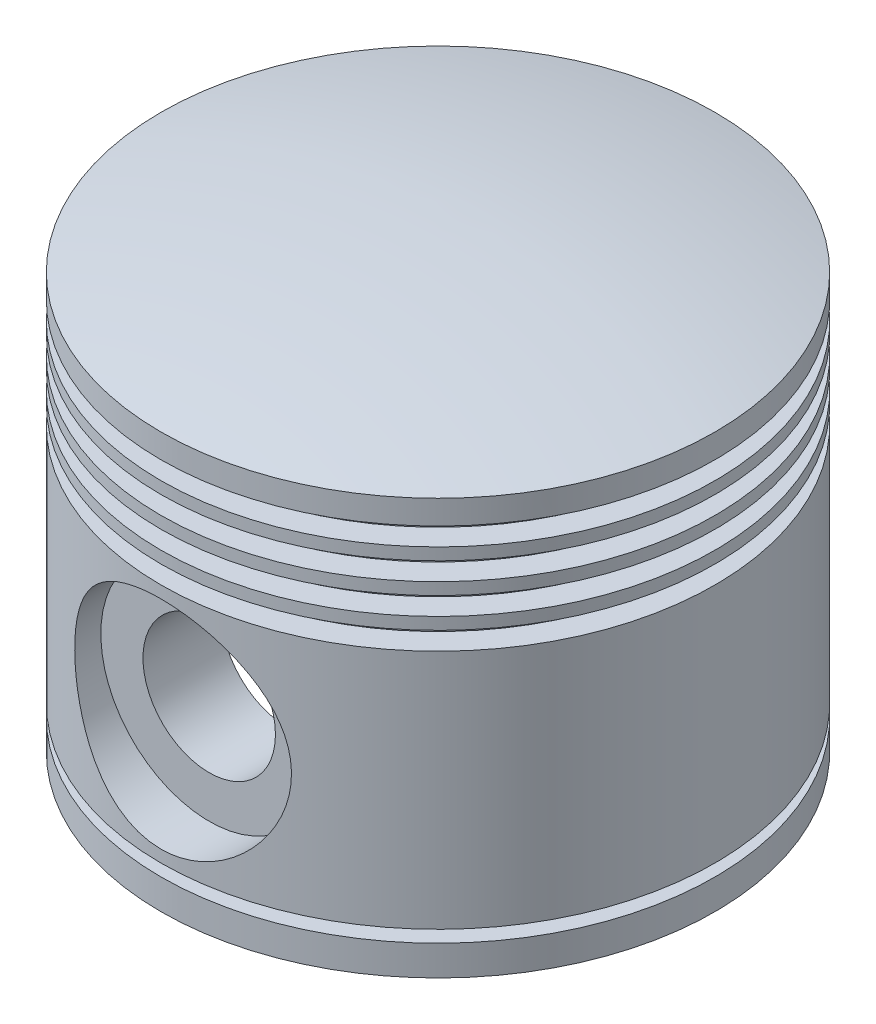
SolidWorks part; units mm, degrees
ref_plane "Front Plane" through (0, 0, 0) normal (0, 0, 1) x (1, 0, 0)
ref_plane "Top Plane" through (0, 0, 0) normal (0, 1, 0) x (1, 0, 0)
ref_plane "Right Plane" through (0, 0, 0) normal (1, 0, 0) x (0, 0, -1)
sketch "Sketch1" plane through (0, 0, 0) normal (0, 0, 1) x (1, 0, 0)
  line L0 (0, 165.4439) -> (0, -165.4439) construction
  line L1 (-46, 0) -> (46, 0) construction
  line L2 (-46, 0) -> (-46, 5)
  line L3 (-46, 5) -> (-42, 5)
  line L4 (-42, 5) -> (-42, 7)
  line L5 (-42, 7) -> (-46, 7)
  line L6 (-46, 7) -> (-46, 9)
  line L10 (-46, 45) -> (-46, 47)
  line L11 (-46, 47) -> (-42, 47)
  line L12 (-42, 47) -> (-42, 50)
  line L13 (-42, 50) -> (-46, 50)
  line L14 (-46, 50) -> (-46, 52)
  line L15 (-46, 52) -> (-42, 52)
  line L16 (-42, 52) -> (-42, 55)
  line L17 (-42, 55) -> (-46, 55)
  line L18 (-46, 55) -> (-46, 57)
  line L19 (-46, 57) -> (-42, 57)
  line L20 (-42, 57) -> (-42, 60)
  line L21 (-42, 60) -> (-46, 60)
  line L22 (-46, 60) -> (-46, 62)
  line L23 (-46, 62) -> (-42, 62)
  line L24 (-42, 62) -> (-42, 65)
  line L25 (-42, 65) -> (-46, 65)
  line L26 (-46, 65) -> (-46, 69)
  line L28 (0, 60) -> (-37, 60)
  line L29 (-37, 60) -> (-37, 47)
  line L33 (-37, 9) -> (-37, 0)
  line L34 (-37, 0) -> (-46, 0)
  line L35 (0, 69) -> (0, 60)
  line L36 (-46, 69) -> (0, 69) construction
  line L37 (46, 69) -> (46, 0) construction
  line L38 (0, 69) -> (46, 69) construction
  line L39 (0, 69) -> (0, 74.6833)
  line L40 (-37, 47) -> (-37, 9)
  line L41 (-46, 45) -> (-46, 9)
  arc A0 (-46, 69) -> (0, 74.6833) centre (0, -114.3167) cw
  point P5 (0, 0)
  point P30 (-44, 60)
  dimension "D18" = 69
  dimension "D15" = 189
  dimension "D1" = 46
  dimension "D2" = 4
  dimension "D3" = 5
  dimension "D4" = 7
  dimension "D8" = 3
  dimension "D9" = 2
  dimension "D10" = 3
  dimension "D11" = 2
  dimension "D12" = 3
  dimension "D13" = 2
  dimension "D14" = 3
  dimension "D16" = 37
  dimension "D19" = 74.6833
revolve "Revolve1" add sketch "Sketch1" angle 360 about L0
sketch "Sketch19" plane through (0, 0, 0) normal (0, 0, 1) x (1, 0, 0)
  line L0 (0, 7) -> (0, 47) construction
  circle A0 centre (0, 27) radius 11
  dimension "D1" = 22
  dimension "D2" = 27
extrude "Cut-Extrude4" cut sketch "Sketch19" against normal through all both and the other way through all
sketch "Sketch20" plane through (0, 0, 0) normal (0, 0, 1) x (1, 0, 0)
  circle A0 centre (0, 27) radius 18
  dimension "D1" = 36
extrude "Cut-Extrude5" cut sketch "Sketch20" against normal blind 4 and the other way through all from offset 42
mirror "Mirror1" about plane through (0, 0, 0) normal (0, 0, 1) of "Cut-Extrude5"
sketch "Sketch21" plane through (0, 0, 0) normal (0, 0, 1) x (1, 0, 0)
  circle A0 centre (0, 27) radius 18
  circle A1 centre (0, 27) radius 11
  dimension "D1" = 22
  dimension "D2" = 36
extrude "Boss-Extrude2" add sketch "Sketch21" against normal up to surface (7.3265 mm away) from offset 25
mirror "Mirror2" about plane through (0, 0, 0) normal (0, 0, 1) of "Boss-Extrude2"
